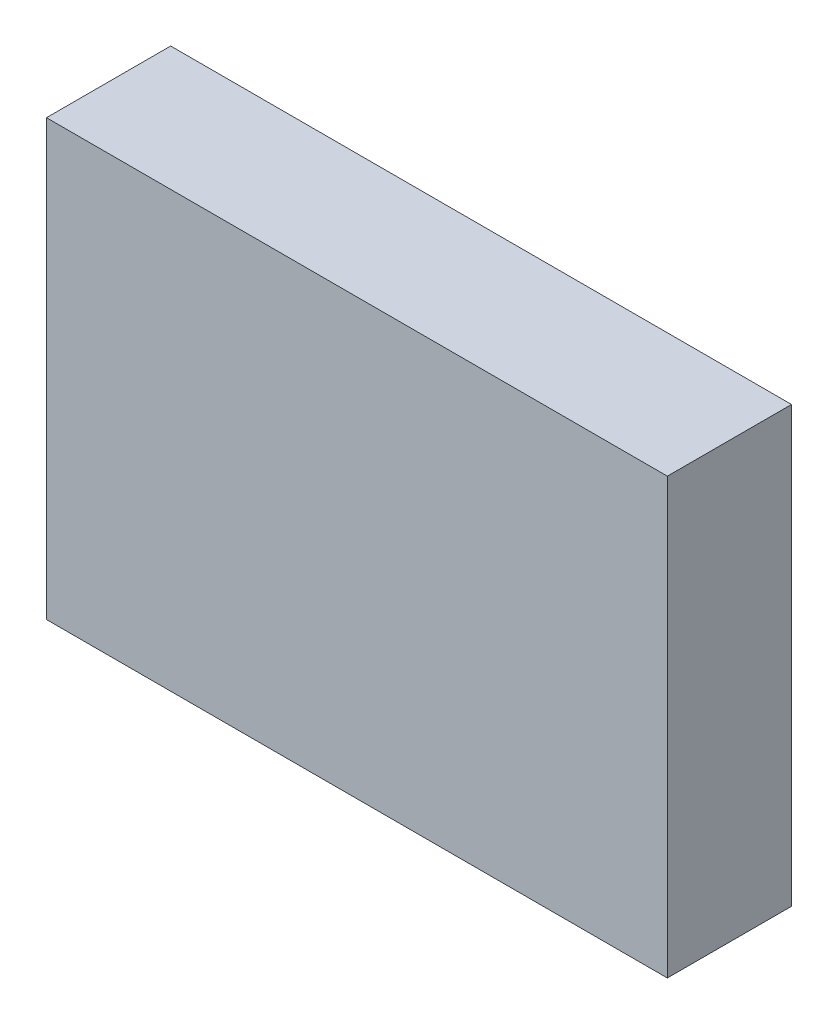
SolidWorks part; units mm, degrees
ref_plane "Front Plane" through (0, 0, 0) normal (0, 0, 1) x (1, 0, 0)
ref_plane "Top Plane" through (0, 0, 0) normal (0, 1, 0) x (1, 0, 0)
ref_plane "Right Plane" through (0, 0, 0) normal (1, 0, 0) x (0, 0, -1)
sketch "Sketch1" plane through (0, 0, 0) normal (0, 1, 0) x (1, 0, 0)
  line L1 (0, 0) -> (10, 0)
  line L2 (0, 0) -> (0, 2)
  line L3 (0, 2) -> (10, 2)
  line L4 (10, 0) -> (10, 2)
extrude "Boss-Extrude1" add sketch "Sketch1" along normal blind 7
